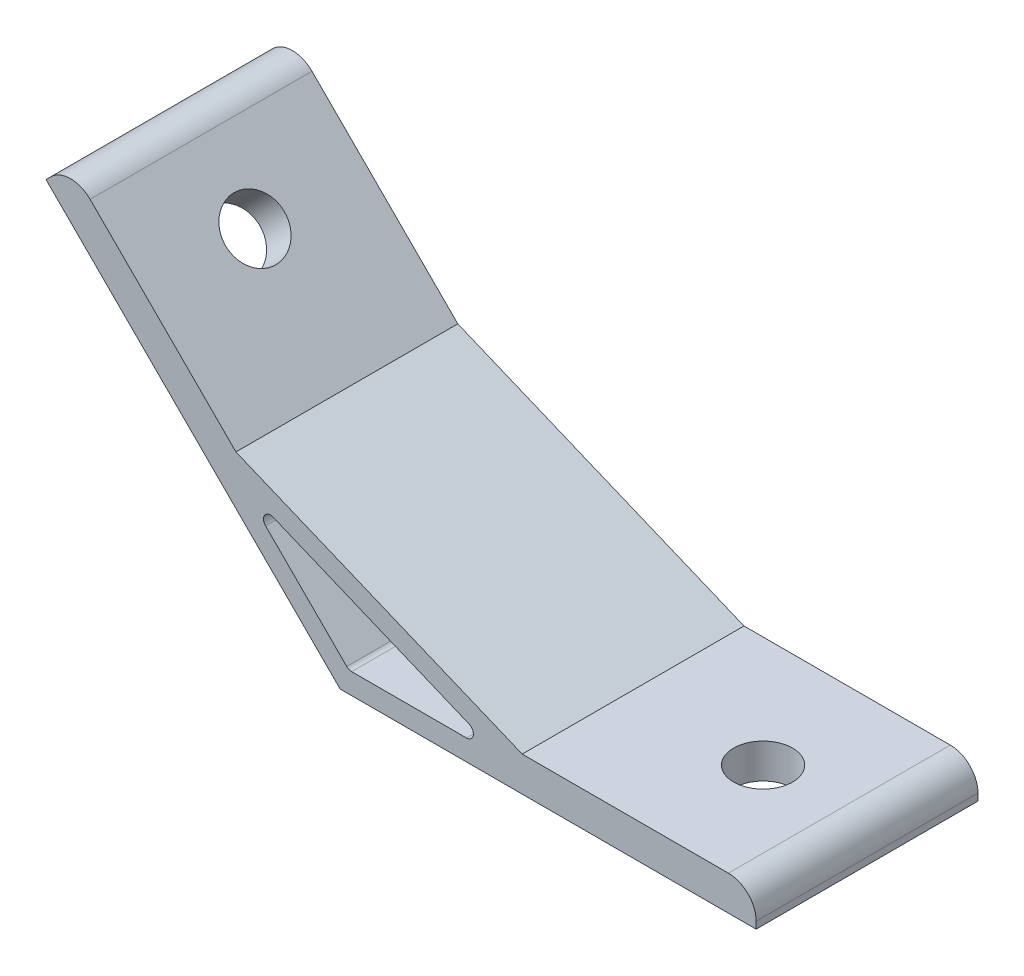
SolidWorks part; units mm, degrees
material "6063 T5"
ref_plane "Спереди" through (0, 0, 0) normal (0, 0, 1) x (1, 0, 0)
ref_plane "Сверху" through (0, 0, 0) normal (0, 1, 0) x (1, 0, 0)
ref_plane "Справа" through (0, 0, 0) normal (1, 0, 0) x (0, 0, -1)
sketch "Эскиз1" plane through (0, 0, 0) normal (0, 0, 1) x (1, 0, 0)
  line L0 (0, 0) -> (-42.4264, 42.4264)
  line L1 (-42.4264, 42.4264) -> (-38.8909, 45.9619)
  line L2 (-38.8909, 45.9619) -> (-15.0286, 22.0996)
  line L3 (-15.0286, 22.0996) -> (26.2536, 5)
  line L4 (26.2536, 5) -> (60, 5)
  line L5 (60, 5) -> (60, 0)
  line L6 (60, 0) -> (0, 0)
  line L7 (-14.3137, 18.5563) -> (23.2426, 3)
  line L8 (23.2426, 3) -> (1.2426, 3)
  line L9 (1.2426, 3) -> (-14.3137, 18.5563)
  line L10 (12.2426, 3) -> (12.2426, 0) construction
  line L11 (-6.5355, 10.7782) -> (-8.6569, 8.6569) construction
  line L12 (0, 0) -> (4.4645, 10.7782) construction
  dimension "D1" = 60
  dimension "D2" = 135
  dimension "D3" = 3
  dimension "D4" = 5
  dimension "D5" = 3
  dimension "D6" = 22
extrude "Бобышка-Вытянуть1" add sketch "Эскиз1" along normal mid plane 32
sketch "Эскиз2" plane through (0, 0, 0) normal (-0.7071, -0.7071, 0) x (0, 0, 1)
  line L0 (16, 60) -> (-16, 60) construction
  circle A0 centre (0, 45) radius 4.25
  dimension "D1" = 8.5
  dimension "D2" = 15
extrude "Вырез-Вытянуть1" cut sketch "Эскиз2" against normal up to surface (5 mm away) up to face at (-26.9597, 34.0308, 0)
sketch "Эскиз3" plane through (0, 0, 0) normal (0, -1, 0) x (1, 0, 0)
  line L0 (60, 16) -> (60, -16) construction
  circle A0 centre (45, 0) radius 4.25
  dimension "D1" = 8.5
  dimension "D2" = 15
extrude "Вырез-Вытянуть2" cut sketch "Эскиз3" against normal up to surface (5 mm away) up to face at (43.1268, 5, 0)
fillet "Скругление1" radius 4 2 edges at (60, 5, 0) (-38.8909, 45.9619, 0)
fillet "Скругление2" radius 1 3 edges at (-14.3137, 18.5563, 0) (1.2426, 3, 0) (23.2426, 3, 0)
